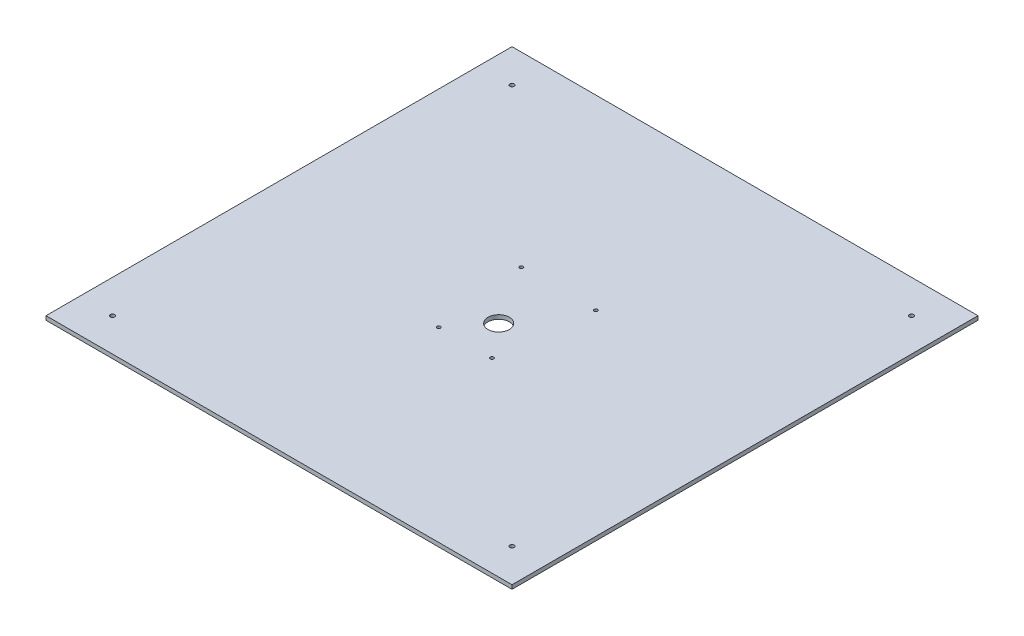
SolidWorks part; units mm, degrees
ref_plane "Front Plane" through (0, 0, 0) normal (0, 0, 1) x (1, 0, 0)
ref_plane "Top Plane" through (0, 0, 0) normal (0, 1, 0) x (1, 0, 0)
ref_plane "Right Plane" through (0, 0, 0) normal (1, 0, 0) x (0, 0, -1)
sketch "Sketch1" plane through (0, 0, 0) normal (0, 1, 0) x (1, 0, 0)
  line L1 (-175, -175) -> (175, -175)
  line L2 (-175, -175) -> (-175, 175)
  line L3 (-175, 175) -> (175, 175)
  line L4 (175, -175) -> (175, 175)
  line L5 (-175, -175) -> (175, 175) construction
  line L6 (-175, 175) -> (175, -175) construction
  circle A0 centre (-150, 150) radius 1.6
  circle A1 centre (-150, -150) radius 1.6
  circle A3 centre (150, -150) radius 1.6
  circle A5 centre (150, 150) radius 1.6
  point P0 (0, 0)
  dimension "D1" = 350
  dimension "D2" = 350
extrude "Boss-Extrude1" add sketch "Sketch1" along normal blind 3
sketch "Sketch2" plane through (0, 3, 0) normal (0, 1, 0) x (1, 0, 0)
  line L0 (0, 35) -> (0, -35) construction
  line L11 (-28, 35) -> (28, 35) construction
  line L13 (20, -35) -> (-20, -35) construction
  circle A1 centre (0, -10) radius 8
  circle A20 centre (-28, 35) radius 1.3
  circle A21 centre (28, 35) radius 1.3
  circle A22 centre (-20, -35) radius 1.3
  circle A23 centre (20, -35) radius 1.3
extrude "Cut-Extrude1" cut sketch "Sketch2" against normal blind 3
